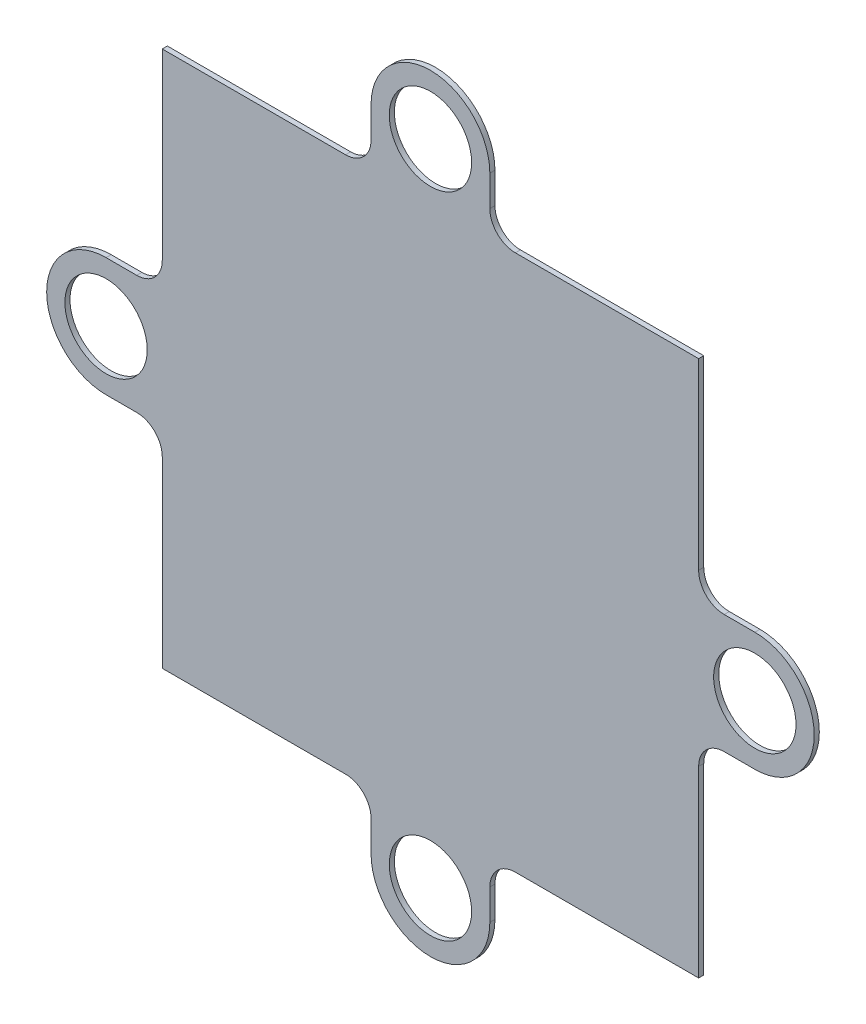
SolidWorks part; units mm, degrees
ref_plane "Front Plane" through (0, 0, 0) normal (0, 0, 1) x (1, 0, 0)
ref_plane "Top Plane" through (0, 0, 0) normal (0, 1, 0) x (1, 0, 0)
ref_plane "Right Plane" through (0, 0, 0) normal (1, 0, 0) x (0, 0, -1)
sketch "Sketch1" plane through (0, 0, 0) normal (0, 0, 1) x (1, 0, 0)
  line L0 (-4.65, 25.4) -> (-4.65, 23)
  line L1 (-21, -21) -> (-6.65, -21)
  line L2 (-21, -21) -> (-21, -6.65)
  line L3 (-21, 21) -> (-6.65, 21)
  line L4 (21, -21) -> (21, -6.65)
  line L5 (-21, -21) -> (21, 21) construction
  line L6 (-21, 21) -> (21, -21) construction
  line L7 (-6.65, 21) -> (-8.7591, 21)
  line L8 (4.65, 25.4) -> (4.65, 23)
  line L9 (6.65, 21) -> (7.1335, 21)
  line L10 (25.4, 4.65) -> (23, 4.65)
  line L11 (21, 6.65) -> (21, 8.7591)
  line L12 (25.4, -4.65) -> (23, -4.65)
  line L13 (21, -6.65) -> (21, -7.1335)
  line L14 (4.65, -25.4) -> (4.65, -23)
  line L15 (6.65, -21) -> (8.7591, -21)
  line L16 (-4.65, -25.4) -> (-4.65, -23)
  line L17 (-6.65, -21) -> (-7.1335, -21)
  line L18 (-25.4, -4.65) -> (-23, -4.65)
  line L19 (-21, -6.65) -> (-21, -8.7591)
  line L20 (-25.4, 4.65) -> (-23, 4.65)
  line L21 (-21, 6.65) -> (-21, 7.1335)
  line L22 (-21, 6.65) -> (-21, 21)
  line L23 (6.65, 21) -> (21, 21)
  line L24 (21, 6.65) -> (21, 21)
  line L25 (6.65, -21) -> (21, -21)
  circle A0 centre (0, 25.4) radius 3.225
  arc A1 (4.65, 25.4) -> (-4.65, 25.4) centre (0, 25.4) ccw
  arc A2 (4.65, 23) -> (6.65, 21) centre (6.65, 23) ccw
  arc A3 (-4.65, 23) -> (-6.65, 21) centre (-6.65, 23) cw
  circle A4 centre (25.4, 0) radius 3.225
  arc A5 (25.4, -4.65) -> (25.4, 4.65) centre (25.4, 0) ccw
  arc A6 (23, -4.65) -> (21, -6.65) centre (23, -6.65) ccw
  arc A7 (23, 4.65) -> (21, 6.65) centre (23, 6.65) cw
  circle A8 centre (0, -25.4) radius 3.225
  arc A9 (-4.65, -25.4) -> (4.65, -25.4) centre (0, -25.4) ccw
  arc A10 (-4.65, -23) -> (-6.65, -21) centre (-6.65, -23) ccw
  arc A11 (4.65, -23) -> (6.65, -21) centre (6.65, -23) cw
  circle A12 centre (-25.4, 0) radius 3.225
  arc A13 (-25.4, 4.65) -> (-25.4, -4.65) centre (-25.4, 0) ccw
  arc A14 (-23, 4.65) -> (-21, 6.65) centre (-23, 6.65) ccw
  arc A15 (-23, -4.65) -> (-21, -6.65) centre (-23, -6.65) cw
  point P0 (0, 0)
  point P53 (0, 0)
  dimension "D1" = 2
extrude "Boss-Extrude1" add sketch "Sketch1" along normal blind 0.4 contours L18 A15 L2 L1 A10 L16 A9 L14 A11 L15 L25 L4 A6 L12 A5 L10 A7 L11 L24 L23 L9 A2 L8 A1 L0 A3 L3 L22 L21 A14 L20 A13 A0 A4 A8 A12
